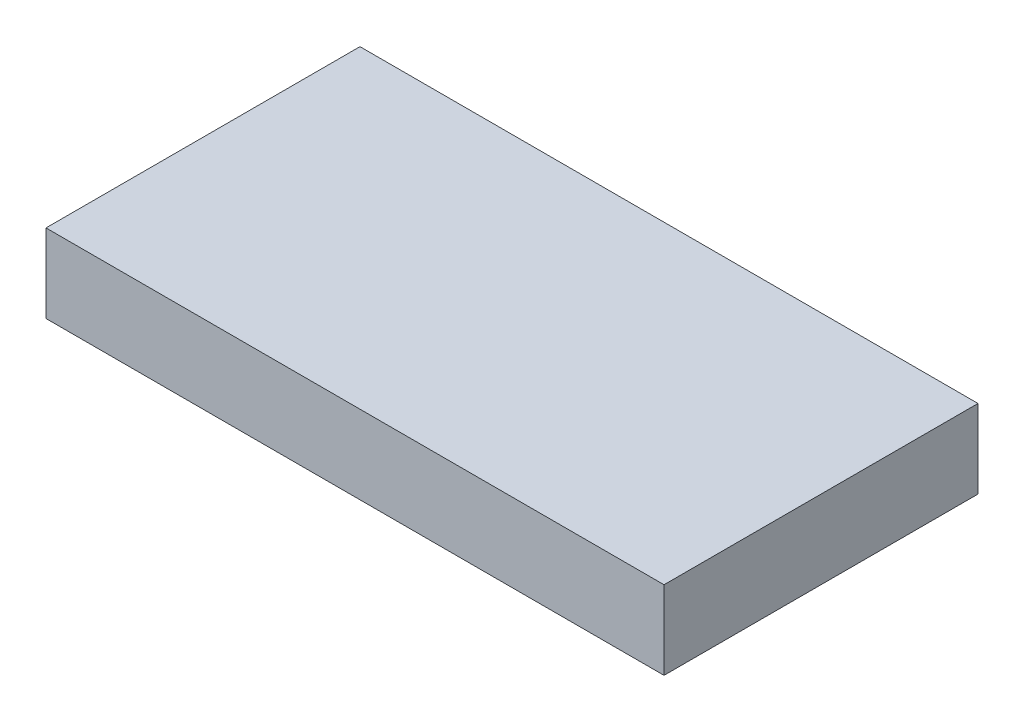
SolidWorks part; units mm, degrees
ref_plane "Front Plane" through (0, 0, 0) normal (0, 0, 1) x (1, 0, 0)
ref_plane "Top Plane" through (0, 0, 0) normal (0, 1, 0) x (1, 0, 0)
ref_plane "Right Plane" through (0, 0, 0) normal (1, 0, 0) x (0, 0, -1)
sketch "Sketch1" plane through (0, 0, 0) normal (0, 1, 0) x (1, 0, 0)
  line L1 (0, 0) -> (200, 0)
  line L2 (0, 0) -> (0, 101.6)
  line L3 (0, 101.6) -> (200, 101.6)
  line L4 (200, 0) -> (200, 101.6)
  dimension "D1" = 200
  dimension "D2" = 101.6
extrude "Boss-Extrude1" add sketch "Sketch1" along normal blind 25.4
